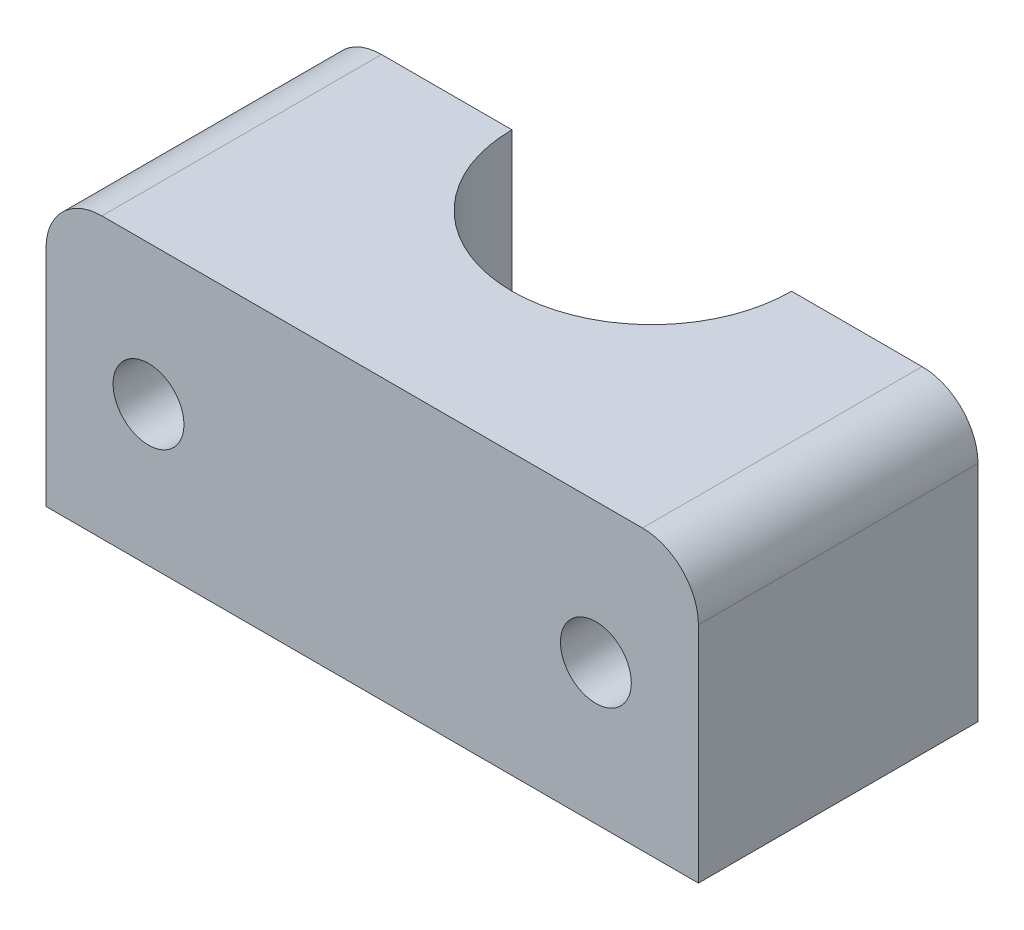
SolidWorks part; units mm, degrees
ref_plane "Front Plane" through (0, 0, 0) normal (0, 0, 1) x (1, 0, 0)
ref_plane "Top Plane" through (0, 0, 0) normal (0, 1, 0) x (1, 0, 0)
ref_plane "Right Plane" through (0, 0, 0) normal (1, 0, 0) x (0, 0, -1)
sketch "Sketch1" plane through (0, 0, 0) normal (0, 0, 1) x (1, 0, 0)
  line L1 (-17.5, 7.5) -> (17.5, 7.5)
  line L2 (-17.5, 7.5) -> (-17.5, -7.5)
  line L3 (-17.5, -7.5) -> (17.5, -7.5)
  line L4 (17.5, 7.5) -> (17.5, -7.5)
  point P4 (0, 7.5)
  point P6 (-17.5, 0)
  dimension "D1" = 35
  dimension "D2" = 15
extrude "Boss-Extrude1" add sketch "Sketch1" along normal blind 15
sketch "Sketch2" plane through (0, 0, 15) normal (0, 0, 1) x (1, 0, 0)
  line L1 (-17.5, -7.5) -> (17.5, -7.5) construction
  circle A0 centre (-12, 0) radius 1.9
  circle A1 centre (12, 0) radius 1.9
  dimension "D3" = 3.8
  dimension "D1" = 12
  dimension "D2" = 12
  dimension "D4" = 7.5
extrude "Cut-Extrude1" cut sketch "Sketch2" against normal blind 15
fillet "Fillet1" radius 3 2 edges at (-17.5, 7.5, 7.5) (17.5, 7.5, 7.5)
sketch "Sketch3" plane through (0, 7.5, 0) normal (0, 1, 0) x (1, 0, 0)
  line L0 (14.5, 0) -> (-14.5, 0) construction
  circle A0 centre (0, 0) radius 7.5
  dimension "D1" = 15
extrude "Cut-Extrude2" cut sketch "Sketch3" against normal through all contours A0
